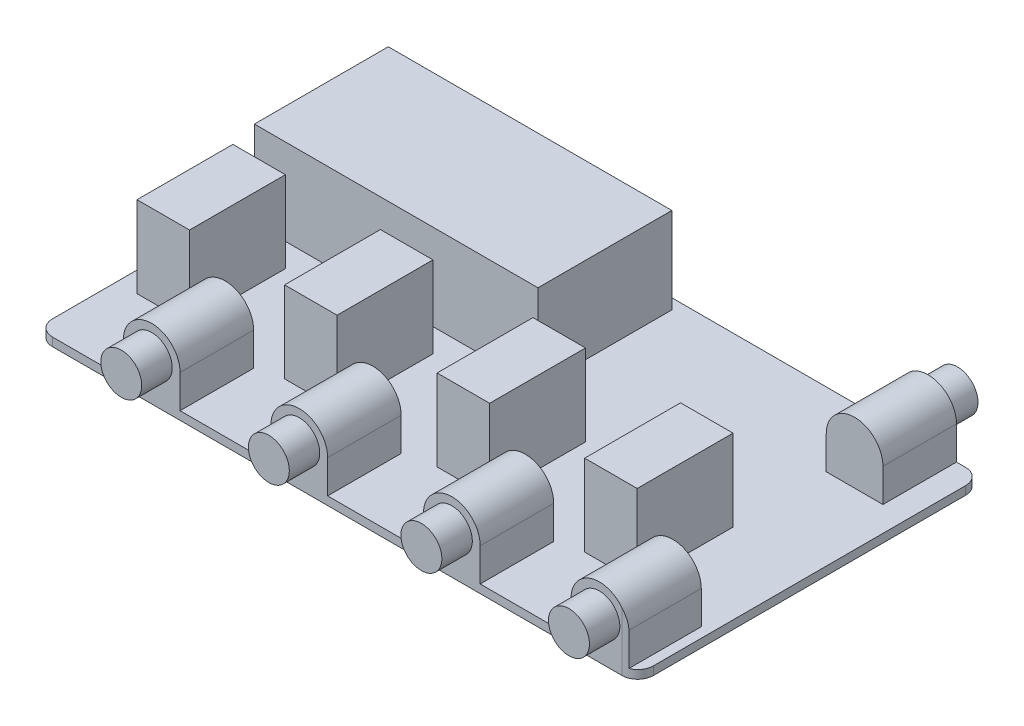
SolidWorks part; units mm, degrees
ref_plane "Plan de face" through (0, 0, 0) normal (0, 0, 1) x (1, 0, 0)
ref_plane "Plan de dessus" through (0, 0, 0) normal (0, 1, 0) x (1, 0, 0)
ref_plane "Plan de droite" through (0, 0, 0) normal (1, 0, 0) x (0, 0, -1)
sketch "Esquisse1" plane through (0, 0, 0) normal (0, 1, 0) x (1, 0, 0)
  line L1 (-57.225, -32.725) -> (57.225, -32.725)
  line L2 (-57.225, -32.725) -> (-57.225, 32.725)
  line L3 (-57.225, 32.725) -> (57.225, 32.725)
  line L4 (57.225, -32.725) -> (57.225, 32.725)
  line L5 (-57.225, -32.725) -> (57.225, 32.725) construction
  line L6 (-57.225, 32.725) -> (57.225, -32.725) construction
  point P0 (0, 0)
  dimension "D1" = 114.45
  dimension "D2" = 65.45
extrude "Boss.-Extru.1" add sketch "Esquisse1" along normal blind 1.6
sketch "Esquisse2" plane through (0, 0, 32.725) normal (0, 0, 1) x (1, 0, 0)
  line L0 (-57.225, 1.6) -> (57.225, 1.6) construction
  line L1 (44.525, 1.6) -> (55.325, 1.6)
  line L2 (44.525, 1.6) -> (44.525, 7.9)
  line L4 (55.325, 1.6) -> (55.325, 7.9)
  line L6 (57.225, 1.6) -> (57.225, 0) construction
  arc A0 (44.525, 7.9) -> (55.325, 7.9) centre (49.925, 7.9) cw
  point P8 (0, 0)
  point P10 (45.6949, 4.5435)
  dimension "D2" = 5.4
  dimension "D1" = 6.3
  dimension "D3" = 1.9
extrude "Boss.-Extru.2" add sketch "Esquisse2" against normal blind 14
sketch "Esquisse3" plane through (0, 0, 32.725) normal (0, 0, 1) x (1, 0, 0)
  circle A0 centre (49.925, 7.9) radius 3.9
  dimension "D1" = 7.8
extrude "Boss.-Extru.3" add sketch "Esquisse3" along normal blind 5.8
sketch "Esquisse6" plane through (0, 1.6, 0) normal (0, 1, 0) x (1, 0, 0)
  line L0 (57.225, 32.725) -> (-57.225, 32.725) construction
  line L1 (31.925, -17.525) -> (41.925, -17.525)
  line L2 (31.925, -17.525) -> (31.925, 0.725)
  line L3 (31.925, 0.725) -> (41.925, 0.725)
  line L4 (41.925, -17.525) -> (41.925, 0.725)
  line L5 (57.225, -32.725) -> (57.225, 32.725) construction
  dimension "D1" = 18.25
  dimension "D2" = 10
  dimension "D3" = 32
  dimension "D4" = 15.3
extrude "Boss.-Extru.6" add sketch "Esquisse6" along normal blind 15.5
pattern_linear "Répétition linéaire1" count 2 spacing 28.1 along (-1, 0, 0) of "Boss.-Extru.3", "Boss.-Extru.2", "Boss.-Extru.6"
pattern_linear "Répétition linéaire2" count 2 spacing 57.15 along (-1, 0, 0) of "Répétition linéaire1", "Boss.-Extru.2", "Boss.-Extru.3", "Boss.-Extru.6"
sketch "Esquisse4" plane through (0, 0, -32.725) normal (0, 0, -1) x (-1, 0, 0)
  line L0 (-57.225, 1.6) -> (57.225, 1.6) construction
  line L1 (-41.675, 1.6) -> (-52.475, 1.6)
  line L2 (-41.675, 1.6) -> (-41.675, 7.9)
  line L4 (-52.475, 1.6) -> (-52.475, 7.9)
  line L5 (-44.525, 7.9) -> (-44.525, 1.6) construction
  line L6 (-57.225, 1.6) -> (-57.225, 0) construction
  arc A0 (-52.475, 7.9) -> (-41.675, 7.9) centre (-47.075, 7.9) cw
  arc A1 (-44.525, 7.9) -> (-55.325, 7.9) centre (-49.925, 7.9) ccw construction
  point P8 (0, 0)
  dimension "D1" = 4.75
extrude "Boss.-Extru.4" add sketch "Esquisse4" against normal blind 14
sketch "Esquisse5" plane through (0, 0, -32.725) normal (0, 0, -1) x (-1, 0, 0)
  circle A0 centre (-47.075, 7.9) radius 3.9
  dimension "D1" = 7.8
extrude "Boss.-Extru.5" add sketch "Esquisse5" along normal blind 5.6
fillet "Congé1" radius 3 4 edges at (57.225, 0.8, -32.725) (-57.225, 0.8, -32.725) (-57.225, 0.8, 32.725) (57.225, 0.8, 32.725)
sketch "Esquisse7" plane through (0, 1.6, 0) normal (0, 1, 0) x (1, 0, 0)
  line L0 (-57.225, 29.725) -> (-57.225, -29.725) construction
  line L1 (-53.725, 30.725) -> (0.275, 30.725)
  line L2 (-53.725, 30.725) -> (-53.725, 5.225)
  line L3 (-53.725, 5.225) -> (0.275, 5.225)
  line L4 (0.275, 30.725) -> (0.275, 5.225)
  line L5 (41.675, 32.725) -> (-54.225, 32.725) construction
  point P6 (0.275, 28.1572)
  dimension "D1" = 25.5
  dimension "D2" = 54
  dimension "D3" = 3.5
  dimension "D4" = 2
extrude "Boss.-Extru.7" add sketch "Esquisse7" along normal blind 16.4
